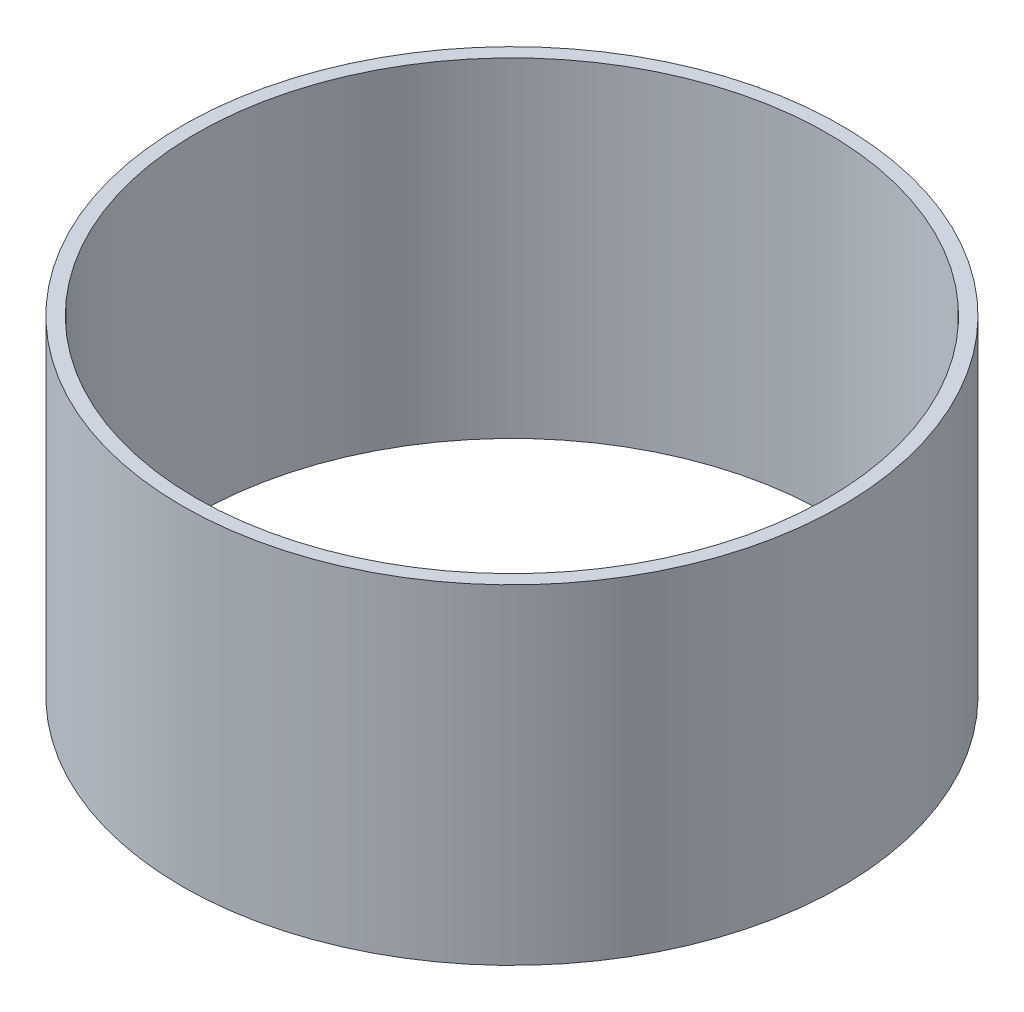
SolidWorks part; units mm, degrees
material "6061-T6 (SS)"
ref_plane "Front Plane" through (0, 0, 0) normal (0, 0, 1) x (1, 0, 0)
ref_plane "Top Plane" through (0, 0, 0) normal (0, 1, 0) x (1, 0, 0)
ref_plane "Right Plane" through (0, 0, 0) normal (1, 0, 0) x (0, 0, -1)
sketch "Sketch1" plane through (0, 0, 0) normal (0, 1, 0) x (1, 0, 0)
  circle A0 centre (0, 0) radius 152.4
  circle A1 centre (0, 0) radius 146.05
  dimension "D1" = 304.8
  dimension "D2" = 6.35
extrude "Boss-Extrude1" add sketch "Sketch1" along normal blind 152.4
